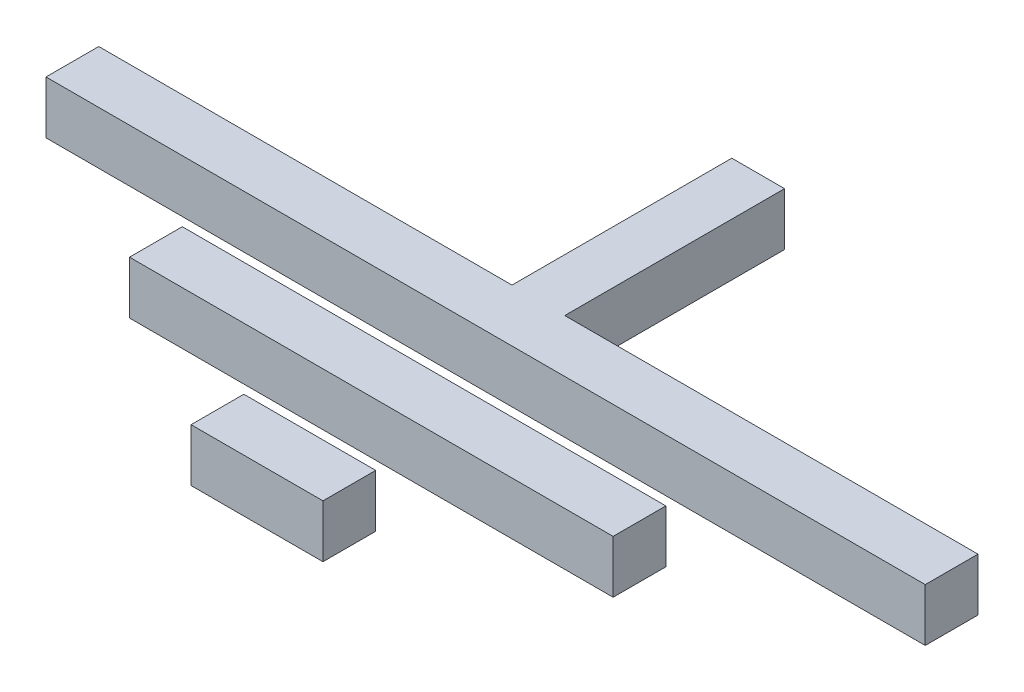
SolidWorks part; units mm, degrees
ref_plane "Front" through (0, 0, 0) normal (0, 0, 1) x (1, 0, 0)
ref_plane "Top" through (0, 0, 0) normal (0, 1, 0) x (1, 0, 0)
ref_plane "Right" through (0, 0, 0) normal (1, 0, 0) x (0, 0, -1)
sketch "Sketch1" plane through (0, 0, 0) normal (0, 1, 0) x (1, 0, 0)
  line L0 (2.5026, 2.3663) -> (8.5026, 2.3663) construction
  line L1 (2.5026, 2.3663) -> (8.5026, 2.3663)
  line L2 (2.5026, 2.3663) -> (2.5026, -22.6337)
  line L3 (2.5026, -22.6337) -> (8.5026, -22.6337)
  line L4 (8.5026, 2.3663) -> (8.5026, -22.6337)
  line L5 (-44.4974, -22.6337) -> (55.5026, -22.6337)
  line L6 (-44.4974, -22.6337) -> (-44.4974, -28.6337)
  line L7 (-44.4974, -28.6337) -> (55.5026, -28.6337)
  line L8 (55.5026, -22.6337) -> (55.5026, -28.6337)
  line L9 (-21.9974, -35.6337) -> (33.0026, -35.6337)
  line L10 (-21.9974, -35.6337) -> (-21.9974, -41.6337)
  line L11 (-21.9974, -41.6337) -> (33.0026, -41.6337)
  line L12 (33.0026, -35.6337) -> (33.0026, -41.6337)
  line L13 (-1.9974, -48.6337) -> (13.0026, -48.6337)
  line L14 (-1.9974, -48.6337) -> (-1.9974, -54.6337)
  line L15 (-1.9974, -54.6337) -> (13.0026, -54.6337)
  line L16 (13.0026, -48.6337) -> (13.0026, -54.6337)
  line L17 (5.5026, 2.3663) -> (5.5026, -39.7853) construction
  point P18 (-83.1759, -5.9153)
  dimension "D1" = 6
  dimension "D2" = 25
  dimension "D3" = 50
  dimension "D4" = 6
  dimension "D5" = 0
  dimension "D6" = 27.5
  dimension "D7" = 55
  dimension "D8" = 6
  dimension "D9" = 7
  dimension "D10" = 6
  dimension "D11" = 15
  dimension "D12" = 7.5
  dimension "D13" = 7
extrude "Boss-Extrude2" add sketch "Sketch1" along normal blind 6 contours L4 L1 L2 L3 | L8 L5 L3 L6 L7 | L12 L9 L10 L11 | L16 L13 L14 L15
